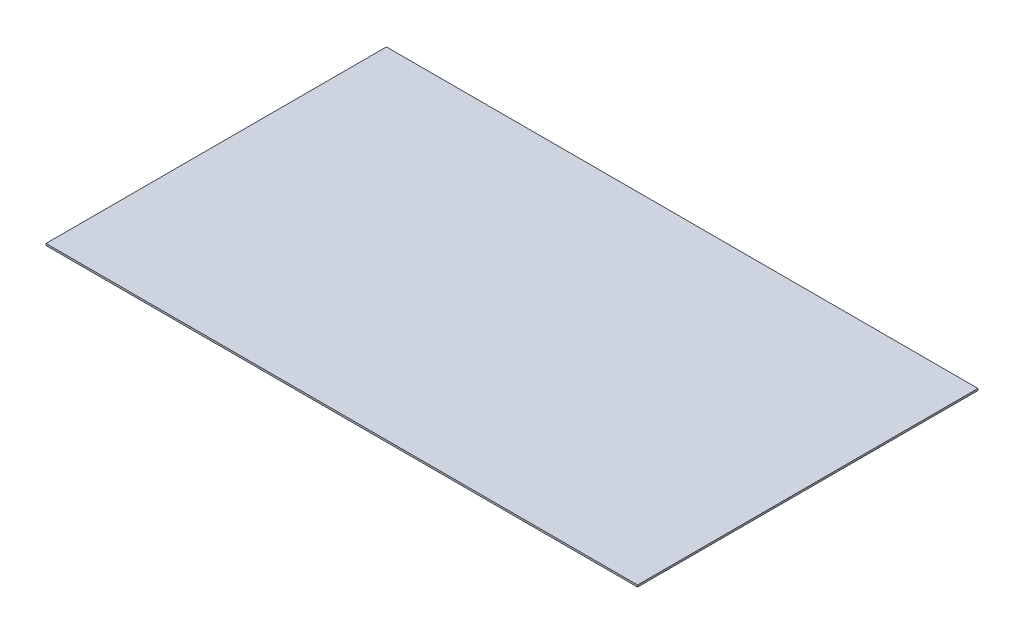
SolidWorks part; units mm, degrees
ref_plane "Front Plane" through (0, 0, 0) normal (0, 0, 1) x (1, 0, 0)
ref_plane "Top Plane" through (0, 0, 0) normal (0, 1, 0) x (1, 0, 0)
ref_plane "Right Plane" through (0, 0, 0) normal (1, 0, 0) x (0, 0, -1)
sketch "Sketch1" plane through (0, 0, 0) normal (0, 1, 0) x (1, 0, 0)
  line L1 (-2996.9131, 1756.0859) -> (213.8539, 1756.0859)
  line L2 (-2996.9131, 1756.0859) -> (-2996.9131, -91.5704)
  line L3 (-2996.9131, -91.5704) -> (213.8539, -91.5704)
  line L4 (213.8539, 1756.0859) -> (213.8539, -91.5704)
  line L5 (-2996.9131, 1756.0859) -> (213.8539, -91.5704) construction
  line L6 (-2996.9131, -91.5704) -> (213.8539, 1756.0859) construction
  point P0 (-1391.5296, 832.2577)
  point P5 (-798.4772, 460.9891)
  point P6 (-2996.9131, 1756.0859)
extrude "Boss-Extrude1" add sketch "Sketch1" along normal blind 10
